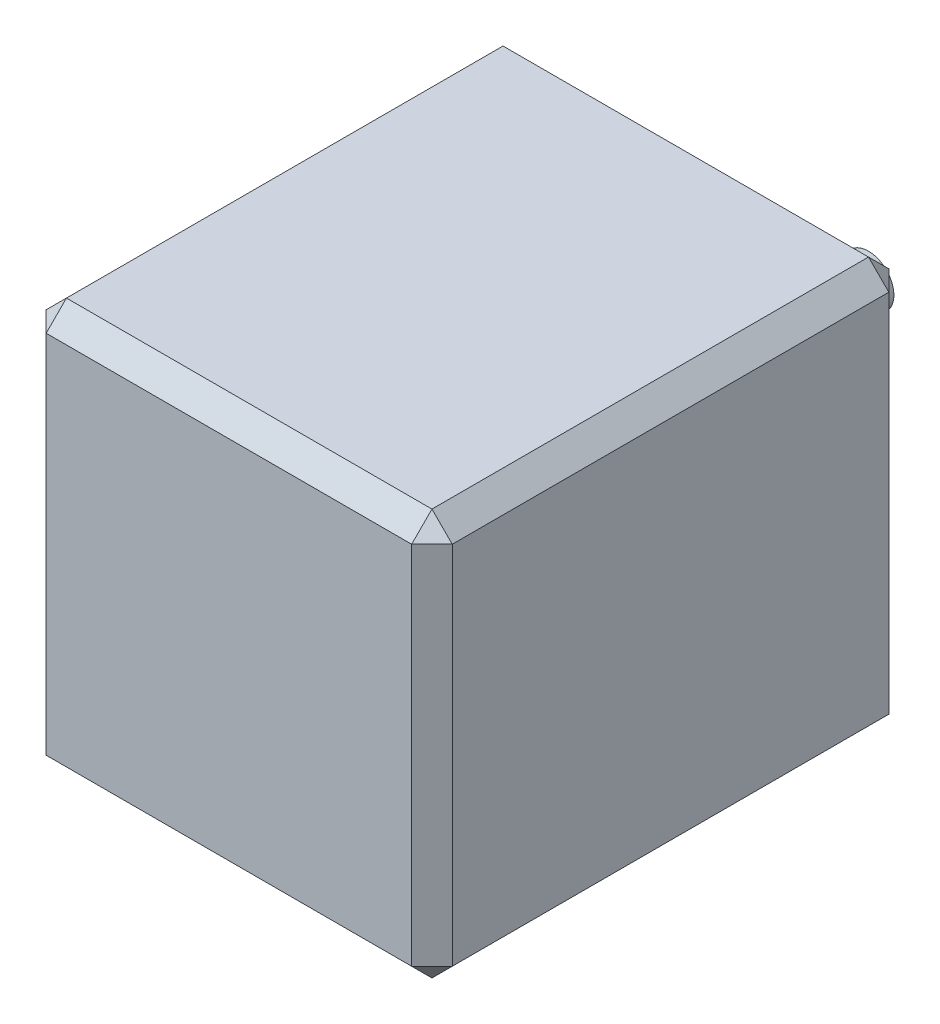
SolidWorks part; units mm, degrees
ref_plane "Front Plane" through (0, 0, 0) normal (0, 0, 1) x (1, 0, 0)
ref_plane "Top Plane" through (0, 0, 0) normal (0, 1, 0) x (1, 0, 0)
ref_plane "Right Plane" through (0, 0, 0) normal (1, 0, 0) x (0, 0, -1)
sketch "Sketch1" plane through (0, 0, 0) normal (0, 0, 1) x (1, 0, 0)
  line L1 (-20, 20) -> (20, 20)
  line L2 (-20, 20) -> (-20, -20)
  line L3 (-20, -20) -> (20, -20)
  line L4 (20, 20) -> (20, -20)
  line L5 (-20, 20) -> (20, -20) construction
  line L6 (-20, -20) -> (20, 20) construction
  point P0 (0, 0)
  dimension "D1" = 40
extrude "Boss-Extrude1" add sketch "Sketch1" along normal mid plane 47
chamfer "Chamfer1" distance 2 angle 45 12 edges at (0, -20, -23.5) (-20, -20, 0) (-20, 0, -23.5) (0, -20, 23.5) (-20, 0, 23.5) (20, -20, 0) (20, 0, 23.5) (20, 0, -23.5) (20, 20, 0) (0, 20, 23.5) (-20, 20, 0) (0, 20, -23.5)
sketch "Sketch2" plane through (0, 0, -23.5) normal (0, 0, -1) x (-1, 0, 0)
  circle A0 centre (0, 0) radius 11
  dimension "D1" = 22
extrude "Boss-Extrude2" add sketch "Sketch2" along normal mid plane 2
sketch "Sketch3" plane through (0, 0, -24.5) normal (0, 0, -1) x (-1, 0, 0)
  circle A0 centre (0, 0) radius 2.5
  dimension "D1" = 5
extrude "Boss-Extrude3" add sketch "Sketch3" along normal mid plane 30
